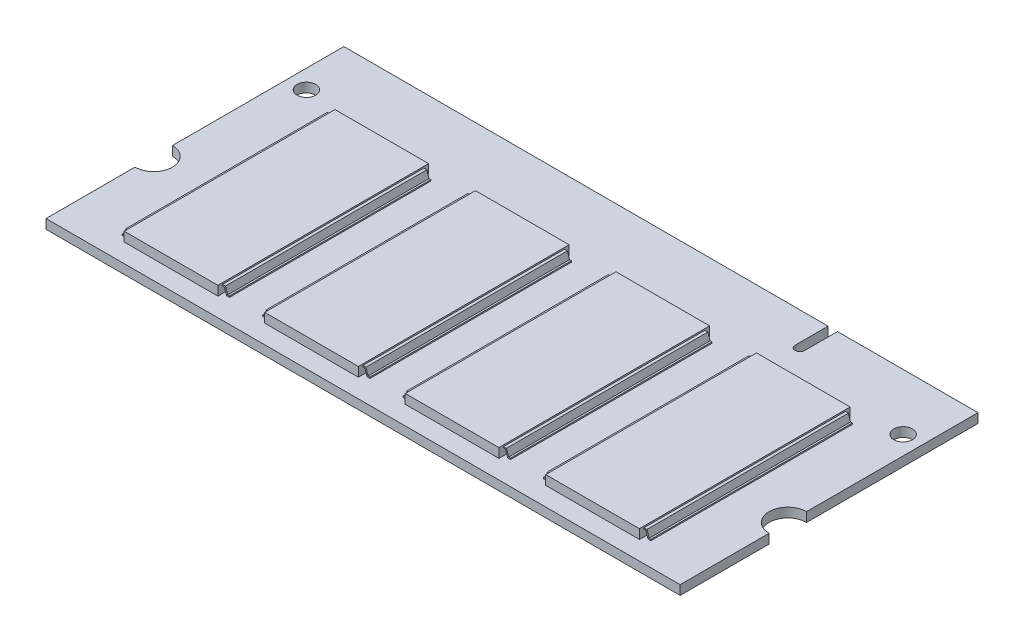
SolidWorks part; units mm, degrees
material "Duranickel(R) 301"
ref_plane "Alzado" through (0, 0, 0) normal (0, 0, 1) x (1, 0, 0)
ref_plane "Planta" through (0, 0, 0) normal (0, 1, 0) x (1, 0, 0)
ref_plane "Vista lateral" through (0, 0, 0) normal (1, 0, 0) x (0, 0, -1)
sketch "Croquis1" plane through (0, 0, 0) normal (0, 1, 0) x (1, 0, 0)
  line L0 (33.85, 9.5) -> (33.85, 0)
  line L1 (-33.85, 31.8) -> (17.85, 31.8)
  line L2 (-33.85, 31.8) -> (-33.85, 13.5)
  line L3 (-33.85, 0) -> (33.85, 0)
  line L4 (33.85, 31.8) -> (33.85, 13.5)
  line L5 (0, 0) -> (0, -18.9694) construction
  line L6 (-33.85, 9.5) -> (-33.85, 0)
  line L7 (18.85, 31.8) -> (33.85, 31.8)
  line L9 (18.85, 31.8) -> (18.85, 28.25)
  line L10 (18.4, 27.8) -> (18.3, 27.8)
  line L11 (17.85, 31.8) -> (17.85, 28.25)
  arc A0 (33.85, 13.5) -> (33.85, 9.5) centre (33.85, 11.5) ccw
  arc A1 (-33.85, 13.5) -> (-33.85, 9.5) centre (-33.85, 11.5) cw
  arc A2 (18.3, 27.8) -> (17.85, 28.25) centre (18.3, 28.25) cw
  arc A3 (18.85, 28.25) -> (18.4, 27.8) centre (18.4, 28.25) cw
  circle A4 centre (31.85, 25.8) radius 1
  circle A5 centre (-31.85, 25.8) radius 1
  point P18 (17.85, 27.8)
  dimension "D4" = 4
  dimension "D8" = 0.45
  dimension "D11" = 2
  dimension "D1" = 67.7
  dimension "D2" = 31.8
  dimension "D3" = 15
  dimension "D5" = 11.5
  dimension "D6" = 1
  dimension "D7" = 4
  dimension "D9" = 2
  dimension "D10" = 6
extrude "Extruir1" add sketch "Croquis1" along normal blind 1
sketch "Croquis2" plane through (0, 1, 0) normal (0, 1, 0) x (-1, 0, 0)
  line L0 (33.85, 0) -> (-33.85, 0) construction
  line L1 (2.5, -2) -> (12.5, -2)
  line L2 (2.5, -2) -> (2.5, -24.5)
  line L3 (2.5, -24.5) -> (12.5, -24.5)
  line L4 (12.5, -2) -> (12.5, -24.5)
  line L5 (17.5, -2) -> (17.5, -24.5)
  line L6 (17.5, -2) -> (27.5, -2)
  line L7 (17.5, -24.5) -> (27.5, -24.5)
  line L8 (27.5, -2) -> (27.5, -24.5)
  line L9 (0, 0) -> (0, 15.9335) construction
  line L10 (-27.5, -2) -> (-27.5, -24.5)
  line L11 (-17.5, -24.5) -> (-27.5, -24.5)
  line L12 (-17.5, -2) -> (-27.5, -2)
  line L13 (-17.5, -2) -> (-17.5, -24.5)
  line L14 (-12.5, -2) -> (-12.5, -24.5)
  line L15 (-2.5, -24.5) -> (-12.5, -24.5)
  line L16 (-2.5, -2) -> (-2.5, -24.5)
  line L17 (-2.5, -2) -> (-12.5, -2)
  dimension "D1" = 10
  dimension "D2" = 22.5
  dimension "D3" = 2.5
  dimension "D4" = 2
extrude "Extruir2" add sketch "Croquis2" along normal blind 1 separate body
ref_plane "Plano1" through (0, 0, -24) normal (0, 0, -1) x (-1, 0, 0)
sketch "Croquis3" plane through (0, 0, -24) normal (0, 0, -1) x (-1, 0, 0)
  line L0 (27.5, 1.8385) -> (27.8096, 1.8385)
  line L1 (27.5, 2) -> (27.5, 1) construction
  line L2 (27.8096, 1.8385) -> (28.043, 1.1382)
  line L3 (28.043, 1.1382) -> (28.2327, 1.1382)
  line L4 (28.2327, 1.1382) -> (28.2327, 1)
  line L5 (-17.85, 1) -> (33.85, 1) construction
  line L6 (28.2327, 1) -> (27.9263, 1)
  line L7 (27.9263, 1) -> (27.6923, 1.7021)
  line L8 (27.6923, 1.7021) -> (27.5, 1.7021)
  line L9 (27.5, 1.7021) -> (27.5, 1.8385)
  line L10 (22.5, 2) -> (22.5, 6.2498) construction
  line L11 (17.5, 2) -> (27.5, 2) construction
  line L12 (17.5, 1.7021) -> (17.5, 1.8385)
  line L13 (17.3077, 1.7021) -> (17.5, 1.7021)
  line L14 (17.0737, 1) -> (17.3077, 1.7021)
  line L15 (16.7673, 1) -> (17.0737, 1)
  line L16 (16.7673, 1.1382) -> (16.7673, 1)
  line L17 (16.957, 1.1382) -> (16.7673, 1.1382)
  line L18 (17.1904, 1.8385) -> (16.957, 1.1382)
  line L19 (17.5, 1.8385) -> (17.1904, 1.8385)
  line L20 (1.7673, 1) -> (2.0737, 1)
  line L21 (2.5, 1.8385) -> (2.1904, 1.8385)
  line L22 (12.8096, 1.8385) -> (13.043, 1.1382)
  line L23 (2.3077, 1.7021) -> (2.5, 1.7021)
  line L24 (2.1904, 1.8385) -> (1.957, 1.1382)
  line L25 (12.6923, 1.7021) -> (12.5, 1.7021)
  line L26 (2.0737, 1) -> (2.3077, 1.7021)
  line L27 (1.7673, 1.1382) -> (1.7673, 1)
  line L28 (13.043, 1.1382) -> (13.2327, 1.1382)
  line L29 (13.2327, 1.1382) -> (13.2327, 1)
  line L30 (12.5, 1.7021) -> (12.5, 1.8385)
  line L31 (12.5, 1.8385) -> (12.8096, 1.8385)
  line L32 (13.2327, 1) -> (12.9263, 1)
  line L33 (2.5, 1.7021) -> (2.5, 1.8385)
  line L34 (1.957, 1.1382) -> (1.7673, 1.1382)
  line L35 (12.9263, 1) -> (12.6923, 1.7021)
  line L36 (-13.2327, 1) -> (-12.9263, 1)
  line L37 (-12.5, 1.8385) -> (-12.8096, 1.8385)
  line L38 (-2.1904, 1.8385) -> (-1.957, 1.1382)
  line L39 (-12.6923, 1.7021) -> (-12.5, 1.7021)
  line L40 (-12.8096, 1.8385) -> (-13.043, 1.1382)
  line L41 (-2.3077, 1.7021) -> (-2.5, 1.7021)
  line L42 (-12.9263, 1) -> (-12.6923, 1.7021)
  line L43 (-13.2327, 1.1382) -> (-13.2327, 1)
  line L44 (-1.957, 1.1382) -> (-1.7673, 1.1382)
  line L45 (-1.7673, 1.1382) -> (-1.7673, 1)
  line L46 (-2.5, 1.7021) -> (-2.5, 1.8385)
  line L47 (-2.5, 1.8385) -> (-2.1904, 1.8385)
  line L48 (-1.7673, 1) -> (-2.0737, 1)
  line L49 (-12.5, 1.7021) -> (-12.5, 1.8385)
  line L50 (-13.043, 1.1382) -> (-13.2327, 1.1382)
  line L51 (-2.0737, 1) -> (-2.3077, 1.7021)
  line L52 (-28.2327, 1) -> (-27.9263, 1)
  line L53 (-27.5, 1.8385) -> (-27.8096, 1.8385)
  line L54 (-17.1904, 1.8385) -> (-16.957, 1.1382)
  line L55 (-27.6923, 1.7021) -> (-27.5, 1.7021)
  line L56 (-27.8096, 1.8385) -> (-28.043, 1.1382)
  line L57 (-17.3077, 1.7021) -> (-17.5, 1.7021)
  line L58 (-27.9263, 1) -> (-27.6923, 1.7021)
  line L59 (-28.2327, 1.1382) -> (-28.2327, 1)
  line L60 (-16.957, 1.1382) -> (-16.7673, 1.1382)
  line L61 (-16.7673, 1.1382) -> (-16.7673, 1)
  line L62 (-17.5, 1.7021) -> (-17.5, 1.8385)
  line L63 (-17.5, 1.8385) -> (-17.1904, 1.8385)
  line L64 (-16.7673, 1) -> (-17.0737, 1)
  line L65 (-27.5, 1.7021) -> (-27.5, 1.8385)
  line L66 (-28.043, 1.1382) -> (-28.2327, 1.1382)
  line L67 (-17.0737, 1) -> (-17.3077, 1.7021)
extrude "Extruir3" add sketch "Croquis3" against normal blind 21.5 separate body
ref_plane "Plano2" through (0, 0.5, 0) normal (0, 1, 0) x (-1, 0, 0)
mirror "Simetría2" about plane through (0, 0.5, 0) normal (0, 1, 0) of bodies 104 105 102 103 108 106 110 112 113 111 109 107
